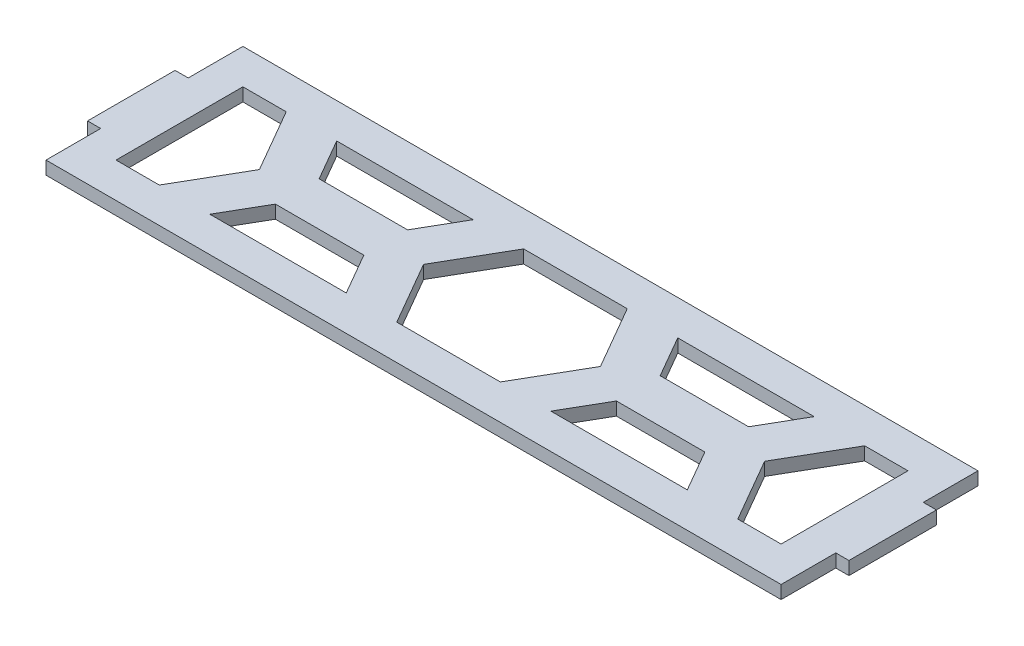
SolidWorks part; units mm, degrees
ref_plane "Front Plane" through (0, 0, 0) normal (0, 0, 1) x (1, 0, 0)
ref_plane "Top Plane" through (0, 0, 0) normal (0, 1, 0) x (1, 0, 0)
ref_plane "Right Plane" through (0, 0, 0) normal (1, 0, 0) x (0, 0, -1)
sketch "Sketch1" plane through (0, 0, 0) normal (0, 1, 0) x (1, 0, 0)
  line L0 (-87, 10) -> (-87, -10)
  line L1 (-87, -10) -> (-84, -10)
  line L2 (-84, -10) -> (-84, -22.5)
  line L3 (-84, -22.5) -> (84, -22.5)
  line L4 (84, -22.5) -> (84, -10)
  line L5 (84, -10) -> (87, -10)
  line L6 (87, -10) -> (87, 10)
  line L7 (87, 10) -> (84, 10)
  line L8 (84, 10) -> (84, 22.5)
  line L9 (84, 22.5) -> (-84, 22.5)
  line L10 (-84, 22.5) -> (-84, 10)
  line L11 (-84, 10) -> (-87, 10)
  point P13 (0, 22.5)
  point P17 (-87, 0)
  dimension "D1" = 168
  dimension "D2" = 3
  dimension "D3" = 20
  dimension "D4" = 45
extrude "Boss-Extrude1" add sketch "Sketch1" along normal mid plane 3
sketch "Sketch3" plane through (0, 0, 0) normal (0, 1, 0) x (1, 0, 0)
  line L0 (-106.8098, -5) -> (-127.0171, -5)
  line L1 (-106.8098, -50) -> (-127.0171, -50)
  line L2 (-127.0171, -50) -> (-137.1207, -67.5)
  line L3 (-137.1207, -67.5) -> (-127.0171, -85)
  line L4 (-127.0171, -85) -> (-106.8098, -85)
  line L5 (-106.8098, -85) -> (-96.7062, -67.5)
  line L6 (-96.7062, -67.5) -> (-106.8098, -50)
  line L13 (-127.0171, -5) -> (-137.1207, -22.5)
  line L14 (-98.1495, -90) -> (-88.0459, -107.5)
  line L15 (-88.0459, -107.5) -> (-67.8387, -107.5)
  line L16 (-67.8387, -107.5) -> (-57.735, -90)
  line L17 (-57.735, -90) -> (-67.8387, -72.5)
  line L18 (-67.8387, -72.5) -> (-88.0459, -72.5)
  line L19 (-88.0459, -72.5) -> (-98.1495, -90)
  line L20 (-137.1207, -22.5) -> (-127.0171, -40)
  line L21 (-127.0171, -40) -> (-106.8098, -40)
  line L22 (-106.8098, -40) -> (-96.7062, -22.5)
  line L23 (-96.7062, -22.5) -> (-106.8098, -5)
  line L24 (-98.1495, -45) -> (-88.0459, -62.5)
  line L25 (-88.0459, -62.5) -> (-67.8387, -62.5)
  line L26 (-67.8387, -62.5) -> (-57.735, -45)
  line L27 (-57.735, -45) -> (-67.8387, -27.5)
  line L28 (-67.8387, -27.5) -> (-88.0459, -27.5)
  line L29 (-88.0459, -27.5) -> (-98.1495, -45)
  line L30 (-106.8098, 40) -> (-127.0171, 40)
  line L31 (-127.0171, 40) -> (-137.1207, 22.5)
  line L32 (-137.1207, 22.5) -> (-127.0171, 5)
  line L33 (-127.0171, 5) -> (-106.8098, 5)
  line L34 (-106.8098, 5) -> (-96.7062, 22.5)
  line L35 (-96.7062, 22.5) -> (-106.8098, 40)
  line L36 (-98.1495, 0) -> (-88.0459, -17.5)
  line L37 (-88.0459, -17.5) -> (-67.8387, -17.5)
  line L38 (-67.8387, -17.5) -> (-57.735, 0)
  line L39 (-57.735, 0) -> (-67.8387, 17.5)
  line L40 (-67.8387, 17.5) -> (-88.0459, 17.5)
  line L41 (-88.0459, 17.5) -> (-98.1495, 0)
  line L42 (-106.8098, 85) -> (-127.0171, 85)
  line L43 (-127.0171, 85) -> (-137.1207, 67.5)
  line L44 (-137.1207, 67.5) -> (-127.0171, 50)
  line L45 (-127.0171, 50) -> (-106.8098, 50)
  line L46 (-106.8098, 50) -> (-96.7062, 67.5)
  line L47 (-96.7062, 67.5) -> (-106.8098, 85)
  line L48 (-98.1495, 45) -> (-88.0459, 27.5)
  line L49 (-88.0459, 27.5) -> (-67.8387, 27.5)
  line L50 (-67.8387, 27.5) -> (-57.735, 45)
  line L51 (-57.735, 45) -> (-67.8387, 62.5)
  line L52 (-67.8387, 62.5) -> (-88.0459, 62.5)
  line L53 (-88.0459, 62.5) -> (-98.1495, 45)
  line L54 (-106.8098, 130) -> (-127.0171, 130)
  line L55 (-127.0171, 130) -> (-137.1207, 112.5)
  line L56 (-137.1207, 112.5) -> (-127.0171, 95)
  line L57 (-127.0171, 95) -> (-106.8098, 95)
  line L58 (-106.8098, 95) -> (-96.7062, 112.5)
  line L59 (-96.7062, 112.5) -> (-106.8098, 130)
  line L60 (-98.1495, 90) -> (-88.0459, 72.5)
  line L61 (-88.0459, 72.5) -> (-67.8387, 72.5)
  line L62 (-67.8387, 72.5) -> (-57.735, 90)
  line L63 (-57.735, 90) -> (-67.8387, 107.5)
  line L64 (-67.8387, 107.5) -> (-88.0459, 107.5)
  line L65 (-88.0459, 107.5) -> (-98.1495, 90)
  line L66 (-106.8098, 175) -> (-127.0171, 175)
  line L67 (-127.0171, 175) -> (-137.1207, 157.5)
  line L68 (-137.1207, 157.5) -> (-127.0171, 140)
  line L69 (-127.0171, 140) -> (-106.8098, 140)
  line L70 (-106.8098, 140) -> (-96.7062, 157.5)
  line L71 (-96.7062, 157.5) -> (-106.8098, 175)
  line L72 (-98.1495, 135) -> (-88.0459, 117.5)
  line L73 (-88.0459, 117.5) -> (-67.8387, 117.5)
  line L74 (-67.8387, 117.5) -> (-57.735, 135)
  line L75 (-57.735, 135) -> (-67.8387, 152.5)
  line L76 (-67.8387, 152.5) -> (-88.0459, 152.5)
  line L77 (-88.0459, 152.5) -> (-98.1495, 135)
  line L102 (-106.8098, -50) -> (-106.8098, -5) construction
  line L103 (-88.0459, -72.5) -> (-88.0459, -62.5) construction
  line L104 (-101.758, -58.75) -> (-93.0977, -53.75) construction
  line L105 (-20.2073, 135) -> (-10.1036, 117.5)
  line L106 (-10.1036, 117.5) -> (10.1036, 117.5)
  line L107 (10.1036, 117.5) -> (20.2073, 135)
  line L108 (20.2073, 135) -> (10.1036, 152.5)
  line L109 (10.1036, 152.5) -> (-10.1036, 152.5)
  line L110 (-10.1036, 152.5) -> (-20.2073, 135)
  line L111 (-28.8675, 175) -> (-49.0748, 175)
  line L112 (-49.0748, 175) -> (-59.1784, 157.5)
  line L113 (-59.1784, 157.5) -> (-49.0748, 140)
  line L114 (-49.0748, 140) -> (-28.8675, 140)
  line L115 (-28.8675, 140) -> (-18.7639, 157.5)
  line L116 (-18.7639, 157.5) -> (-28.8675, 175)
  line L117 (-28.8675, 130) -> (-49.0748, 130)
  line L118 (-49.0748, 130) -> (-59.1784, 112.5)
  line L119 (-59.1784, 112.5) -> (-49.0748, 95)
  line L120 (-49.0748, 95) -> (-28.8675, 95)
  line L121 (-28.8675, 95) -> (-18.7639, 112.5)
  line L122 (-18.7639, 112.5) -> (-28.8675, 130)
  line L123 (-28.8675, 85) -> (-49.0748, 85)
  line L124 (-49.0748, 85) -> (-59.1784, 67.5)
  line L125 (-59.1784, 67.5) -> (-49.0748, 50)
  line L126 (-49.0748, 50) -> (-28.8675, 50)
  line L127 (-28.8675, 50) -> (-18.7639, 67.5)
  line L128 (-18.7639, 67.5) -> (-28.8675, 85)
  line L129 (-28.8675, 40) -> (-49.0748, 40)
  line L130 (-49.0748, 40) -> (-59.1784, 22.5)
  line L131 (-59.1784, 22.5) -> (-49.0748, 5)
  line L132 (-49.0748, 5) -> (-28.8675, 5)
  line L133 (-28.8675, 5) -> (-18.7639, 22.5)
  line L134 (-18.7639, 22.5) -> (-28.8675, 40)
  line L135 (-20.2073, 0) -> (-10.1036, -17.5)
  line L136 (-10.1036, -17.5) -> (10.1036, -17.5)
  line L137 (10.1036, -17.5) -> (20.2073, 0)
  line L138 (20.2073, 0) -> (10.1036, 17.5)
  line L139 (10.1036, 17.5) -> (-10.1036, 17.5)
  line L140 (-10.1036, 17.5) -> (-20.2073, 0)
  line L141 (-28.8675, -5) -> (-49.0748, -5)
  line L142 (-49.0748, -5) -> (-59.1784, -22.5)
  line L143 (-59.1784, -22.5) -> (-49.0748, -40)
  line L144 (-49.0748, -40) -> (-28.8675, -40)
  line L145 (-28.8675, -40) -> (-18.7639, -22.5)
  line L146 (-18.7639, -22.5) -> (-28.8675, -5)
  line L147 (-20.2073, -45) -> (-10.1036, -62.5)
  line L148 (-10.1036, -62.5) -> (10.1036, -62.5)
  line L149 (10.1036, -62.5) -> (20.2073, -45)
  line L150 (20.2073, -45) -> (10.1036, -27.5)
  line L151 (10.1036, -27.5) -> (-10.1036, -27.5)
  line L152 (-10.1036, -27.5) -> (-20.2073, -45)
  line L153 (-28.8675, -50) -> (-49.0748, -50)
  line L154 (-49.0748, -50) -> (-59.1784, -67.5)
  line L155 (-59.1784, -67.5) -> (-49.0748, -85)
  line L156 (-49.0748, -85) -> (-28.8675, -85)
  line L157 (-28.8675, -85) -> (-18.7639, -67.5)
  line L158 (-18.7639, -67.5) -> (-28.8675, -50)
  line L159 (-20.2073, -90) -> (-10.1036, -107.5)
  line L160 (-10.1036, -107.5) -> (10.1036, -107.5)
  line L161 (10.1036, -107.5) -> (20.2073, -90)
  line L162 (20.2073, -90) -> (10.1036, -72.5)
  line L163 (10.1036, -72.5) -> (-10.1036, -72.5)
  line L164 (-10.1036, -72.5) -> (-20.2073, -90)
  line L165 (-20.2073, 45) -> (-10.1036, 27.5)
  line L166 (-10.1036, 27.5) -> (10.1036, 27.5)
  line L167 (10.1036, 27.5) -> (20.2073, 45)
  line L168 (20.2073, 45) -> (10.1036, 62.5)
  line L169 (10.1036, 62.5) -> (-10.1036, 62.5)
  line L170 (-10.1036, 62.5) -> (-20.2073, 45)
  line L171 (-20.2073, 90) -> (-10.1036, 72.5)
  line L172 (-10.1036, 72.5) -> (10.1036, 72.5)
  line L173 (10.1036, 72.5) -> (20.2073, 90)
  line L174 (20.2073, 90) -> (10.1036, 107.5)
  line L175 (10.1036, 107.5) -> (-10.1036, 107.5)
  line L176 (-10.1036, 107.5) -> (-20.2073, 90)
  line L177 (57.735, 135) -> (67.8387, 117.5)
  line L178 (67.8387, 117.5) -> (88.0459, 117.5)
  line L179 (88.0459, 117.5) -> (98.1495, 135)
  line L180 (98.1495, 135) -> (88.0459, 152.5)
  line L181 (88.0459, 152.5) -> (67.8387, 152.5)
  line L182 (67.8387, 152.5) -> (57.735, 135)
  line L183 (49.0748, 175) -> (28.8675, 175)
  line L184 (28.8675, 175) -> (18.7639, 157.5)
  line L185 (18.7639, 157.5) -> (28.8675, 140)
  line L186 (28.8675, 140) -> (49.0748, 140)
  line L187 (49.0748, 140) -> (59.1784, 157.5)
  line L188 (59.1784, 157.5) -> (49.0748, 175)
  line L189 (49.0748, 130) -> (28.8675, 130)
  line L190 (28.8675, 130) -> (18.7639, 112.5)
  line L191 (18.7639, 112.5) -> (28.8675, 95)
  line L192 (28.8675, 95) -> (49.0748, 95)
  line L193 (49.0748, 95) -> (59.1784, 112.5)
  line L194 (59.1784, 112.5) -> (49.0748, 130)
  line L195 (49.0748, 85) -> (28.8675, 85)
  line L196 (28.8675, 85) -> (18.7639, 67.5)
  line L197 (18.7639, 67.5) -> (28.8675, 50)
  line L198 (28.8675, 50) -> (49.0748, 50)
  line L199 (49.0748, 50) -> (59.1784, 67.5)
  line L200 (59.1784, 67.5) -> (49.0748, 85)
  line L201 (49.0748, 40) -> (28.8675, 40)
  line L202 (28.8675, 40) -> (18.7639, 22.5)
  line L203 (18.7639, 22.5) -> (28.8675, 5)
  line L204 (28.8675, 5) -> (49.0748, 5)
  line L205 (49.0748, 5) -> (59.1784, 22.5)
  line L206 (59.1784, 22.5) -> (49.0748, 40)
  line L207 (57.735, 0) -> (67.8387, -17.5)
  line L208 (67.8387, -17.5) -> (88.0459, -17.5)
  line L209 (88.0459, -17.5) -> (98.1495, 0)
  line L210 (98.1495, 0) -> (88.0459, 17.5)
  line L211 (88.0459, 17.5) -> (67.8387, 17.5)
  line L212 (67.8387, 17.5) -> (57.735, 0)
  line L213 (49.0748, -5) -> (28.8675, -5)
  line L214 (28.8675, -5) -> (18.7639, -22.5)
  line L215 (18.7639, -22.5) -> (28.8675, -40)
  line L216 (28.8675, -40) -> (49.0748, -40)
  line L217 (49.0748, -40) -> (59.1784, -22.5)
  line L218 (59.1784, -22.5) -> (49.0748, -5)
  line L219 (57.735, -45) -> (67.8387, -62.5)
  line L220 (67.8387, -62.5) -> (88.0459, -62.5)
  line L221 (88.0459, -62.5) -> (98.1495, -45)
  line L222 (98.1495, -45) -> (88.0459, -27.5)
  line L223 (88.0459, -27.5) -> (67.8387, -27.5)
  line L224 (67.8387, -27.5) -> (57.735, -45)
  line L225 (49.0748, -50) -> (28.8675, -50)
  line L226 (28.8675, -50) -> (18.7639, -67.5)
  line L227 (18.7639, -67.5) -> (28.8675, -85)
  line L228 (28.8675, -85) -> (49.0748, -85)
  line L229 (49.0748, -85) -> (59.1784, -67.5)
  line L230 (59.1784, -67.5) -> (49.0748, -50)
  line L231 (57.735, -90) -> (67.8387, -107.5)
  line L232 (67.8387, -107.5) -> (88.0459, -107.5)
  line L233 (88.0459, -107.5) -> (98.1495, -90)
  line L234 (98.1495, -90) -> (88.0459, -72.5)
  line L235 (88.0459, -72.5) -> (67.8387, -72.5)
  line L236 (67.8387, -72.5) -> (57.735, -90)
  line L237 (57.735, 45) -> (67.8387, 27.5)
  line L238 (67.8387, 27.5) -> (88.0459, 27.5)
  line L239 (88.0459, 27.5) -> (98.1495, 45)
  line L240 (98.1495, 45) -> (88.0459, 62.5)
  line L241 (88.0459, 62.5) -> (67.8387, 62.5)
  line L242 (67.8387, 62.5) -> (57.735, 45)
  line L243 (57.735, 90) -> (67.8387, 72.5)
  line L244 (67.8387, 72.5) -> (88.0459, 72.5)
  line L245 (88.0459, 72.5) -> (98.1495, 90)
  line L246 (98.1495, 90) -> (88.0459, 107.5)
  line L247 (88.0459, 107.5) -> (67.8387, 107.5)
  line L248 (67.8387, 107.5) -> (57.735, 90)
  line L249 (135.6773, 135) -> (145.7809, 117.5)
  line L250 (145.7809, 117.5) -> (165.9882, 117.5)
  line L251 (165.9882, 117.5) -> (176.0918, 135)
  line L252 (176.0918, 135) -> (165.9882, 152.5)
  line L253 (165.9882, 152.5) -> (145.7809, 152.5)
  line L254 (145.7809, 152.5) -> (135.6773, 135)
  line L255 (127.0171, 175) -> (106.8098, 175)
  line L256 (106.8098, 175) -> (96.7062, 157.5)
  line L257 (96.7062, 157.5) -> (106.8098, 140)
  line L258 (106.8098, 140) -> (127.0171, 140)
  line L259 (127.0171, 140) -> (137.1207, 157.5)
  line L260 (137.1207, 157.5) -> (127.0171, 175)
  line L261 (127.0171, 130) -> (106.8098, 130)
  line L262 (106.8098, 130) -> (96.7062, 112.5)
  line L263 (96.7062, 112.5) -> (106.8098, 95)
  line L264 (106.8098, 95) -> (127.0171, 95)
  line L265 (127.0171, 95) -> (137.1207, 112.5)
  line L266 (137.1207, 112.5) -> (127.0171, 130)
  line L267 (127.0171, 85) -> (106.8098, 85)
  line L268 (106.8098, 85) -> (96.7062, 67.5)
  line L269 (96.7062, 67.5) -> (106.8098, 50)
  line L270 (106.8098, 50) -> (127.0171, 50)
  line L271 (127.0171, 50) -> (137.1207, 67.5)
  line L272 (137.1207, 67.5) -> (127.0171, 85)
  line L273 (127.0171, 40) -> (106.8098, 40)
  line L274 (106.8098, 40) -> (96.7062, 22.5)
  line L275 (96.7062, 22.5) -> (106.8098, 5)
  line L276 (106.8098, 5) -> (127.0171, 5)
  line L277 (127.0171, 5) -> (137.1207, 22.5)
  line L278 (137.1207, 22.5) -> (127.0171, 40)
  line L279 (135.6773, 0) -> (145.7809, -17.5)
  line L280 (145.7809, -17.5) -> (165.9882, -17.5)
  line L281 (165.9882, -17.5) -> (176.0918, 0)
  line L282 (176.0918, 0) -> (165.9882, 17.5)
  line L283 (165.9882, 17.5) -> (145.7809, 17.5)
  line L284 (145.7809, 17.5) -> (135.6773, 0)
  line L285 (127.0171, -5) -> (106.8098, -5)
  line L286 (106.8098, -5) -> (96.7062, -22.5)
  line L287 (96.7062, -22.5) -> (106.8098, -40)
  line L288 (106.8098, -40) -> (127.0171, -40)
  line L289 (127.0171, -40) -> (137.1207, -22.5)
  line L290 (137.1207, -22.5) -> (127.0171, -5)
  line L291 (135.6773, -45) -> (145.7809, -62.5)
  line L292 (145.7809, -62.5) -> (165.9882, -62.5)
  line L293 (165.9882, -62.5) -> (176.0918, -45)
  line L294 (176.0918, -45) -> (165.9882, -27.5)
  line L295 (165.9882, -27.5) -> (145.7809, -27.5)
  line L296 (145.7809, -27.5) -> (135.6773, -45)
  line L297 (127.0171, -50) -> (106.8098, -50)
  line L298 (106.8098, -50) -> (96.7062, -67.5)
  line L299 (96.7062, -67.5) -> (106.8098, -85)
  line L300 (106.8098, -85) -> (127.0171, -85)
  line L301 (127.0171, -85) -> (137.1207, -67.5)
  line L302 (137.1207, -67.5) -> (127.0171, -50)
  line L303 (135.6773, -90) -> (145.7809, -107.5)
  line L304 (145.7809, -107.5) -> (165.9882, -107.5)
  line L305 (165.9882, -107.5) -> (176.0918, -90)
  line L306 (176.0918, -90) -> (165.9882, -72.5)
  line L307 (165.9882, -72.5) -> (145.7809, -72.5)
  line L308 (145.7809, -72.5) -> (135.6773, -90)
  line L309 (135.6773, 45) -> (145.7809, 27.5)
  line L310 (145.7809, 27.5) -> (165.9882, 27.5)
  line L311 (165.9882, 27.5) -> (176.0918, 45)
  line L312 (176.0918, 45) -> (165.9882, 62.5)
  line L313 (165.9882, 62.5) -> (145.7809, 62.5)
  line L314 (145.7809, 62.5) -> (135.6773, 45)
  line L315 (135.6773, 90) -> (145.7809, 72.5)
  line L316 (145.7809, 72.5) -> (165.9882, 72.5)
  line L317 (165.9882, 72.5) -> (176.0918, 90)
  line L318 (176.0918, 90) -> (165.9882, 107.5)
  line L319 (165.9882, 107.5) -> (145.7809, 107.5)
  line L320 (145.7809, 107.5) -> (135.6773, 90)
  line L321 (-98.1495, 135) -> (-20.2073, 135) construction
  line L322 (-54.1266, -58.75) -> (-62.7868, -53.75) construction
  line L329 (-87, 10) -> (-87, -10) construction
  line L334 (84, 22.5) -> (-84, 22.5) construction
  line L335 (-76, -14.5) -> (76, -14.5)
  line L336 (-76, -14.5) -> (-76, 14.5)
  line L337 (-76, 14.5) -> (76, 14.5)
  line L338 (76, -14.5) -> (76, 14.5)
  line L339 (-76, -14.5) -> (76, 14.5) construction
  line L340 (-76, 14.5) -> (76, -14.5) construction
  line L341 (84, 10) -> (84, 22.5) construction
  circle A0 centre (-116.9134, -67.5) radius 17.5 construction
  circle A1 centre (-77.9423, -90) radius 17.5 construction
  point P10 (-88.0459, -67.5)
  point P303 (0, 0)
  point P306 (-87, 0)
  point P308 (0, 27.5)
  dimension "D3" = 35
  dimension "D2" = 45
  dimension "D5" = 8
  dimension "D6" = 8
  dimension "D1" = 6
  dimension "D4" = 4
extrude "Cut-Extrude1" cut sketch "Sketch3" against normal through all both and the other way through all contours L337 L336 L335 L38 L39 | L337 L140 L135 L335 L137 L138 | L335 L338 L337 L212 L207 | L214 L335 L218 L213 | L337 L203 L204 L205 | L142 L335 L146 L141 | L337 L131 L132 L133
equation "\"bottomLength\"= 220mm"
equation "\"topLength\"= 330mm"
equation "\"frontHeight\"= 100mm"
equation "\"height\"= 180mm"
equation "\"width\"= 180mm"
equation "\"D1@Sketch1\"=\"width\"-12"
